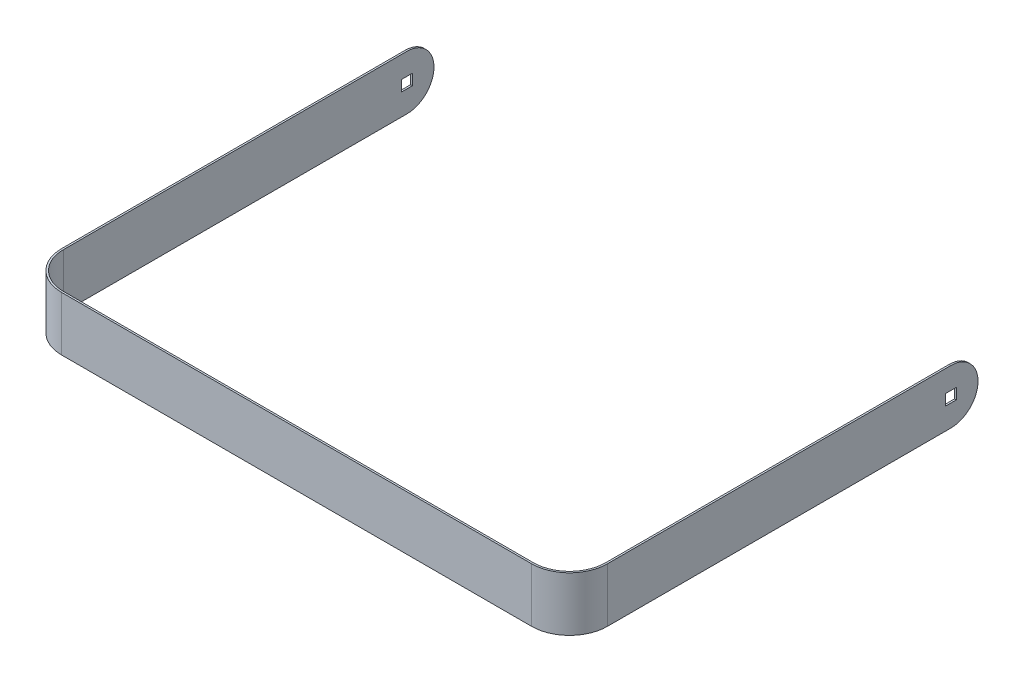
SolidWorks part; units mm, degrees
ref_plane "Ebene vorne" through (0, 0, 0) normal (0, 0, 1) x (1, 0, 0)
ref_plane "Ebene oben" through (0, 0, 0) normal (0, 1, 0) x (1, 0, 0)
ref_plane "Ebene rechts" through (0, 0, 0) normal (1, 0, 0) x (0, 0, -1)
sketch "Skizze3" plane through (0, 0, 0) normal (0, -1, 0) x (1, 0, 0)
  line L0 (-151, -151) -> (-151, -21)
  line L1 (-130, 0) -> (130, 0)
  line L3 (151, -21) -> (151, -151)
  line L4 (151, -151) -> (-151, -151) construction
  line L5 (-151, -151) -> (-151, -226)
  line L6 (151, -151) -> (151, -226)
  line L7 (151, -226) -> (-151, -226) construction
  arc A0 (-151, -21) -> (-130, 0) centre (-130, -21) cw
  arc A1 (130, 0) -> (151, -21) centre (130, -21) cw
  dimension "D1" = 75
extrude "Linear-Austragen-Dünn1" add sketch "Skizze3" along normal blind 30 thin
sketch "Skizze4" plane through (151, 0, 0) normal (1, 0, 0) x (0, 0, -1)
  line L0 (236.9534, 0) -> (211, 0)
  line L1 (21, 0) -> (226, 0) construction
  line L2 (236.9534, 0) -> (236.9534, -30)
  line L3 (236.9534, -30) -> (211, -30)
  line L4 (21, -30) -> (226, -30) construction
  line L5 (226, -30) -> (226, 0) construction
  arc A0 (211, 0) -> (211, -30) centre (211, -15) cw
extrude "Schnitt-Linear austragen1" cut sketch "Skizze4" against normal through all
sketch "Skizze5" plane through (151, 0, 0) normal (1, 0, 0) x (0, 0, -1)
  line L0 (211, 0) -> (211, -30) construction
  line L1 (208, -12) -> (214, -12)
  line L2 (208, -12) -> (208, -18)
  line L3 (208, -18) -> (214, -18)
  line L4 (214, -12) -> (214, -18)
  line L5 (211, -15) -> (226, -15) construction
  line L6 (208, -18) -> (211, -15) construction
  line L7 (211, -15) -> (214, -12) construction
  arc A0 (211, -30) -> (211, 0) centre (211, -15) ccw construction
  dimension "D1" = 6
extrude "Schnitt-Linear austragen2" cut sketch "Skizze5" against normal through all
